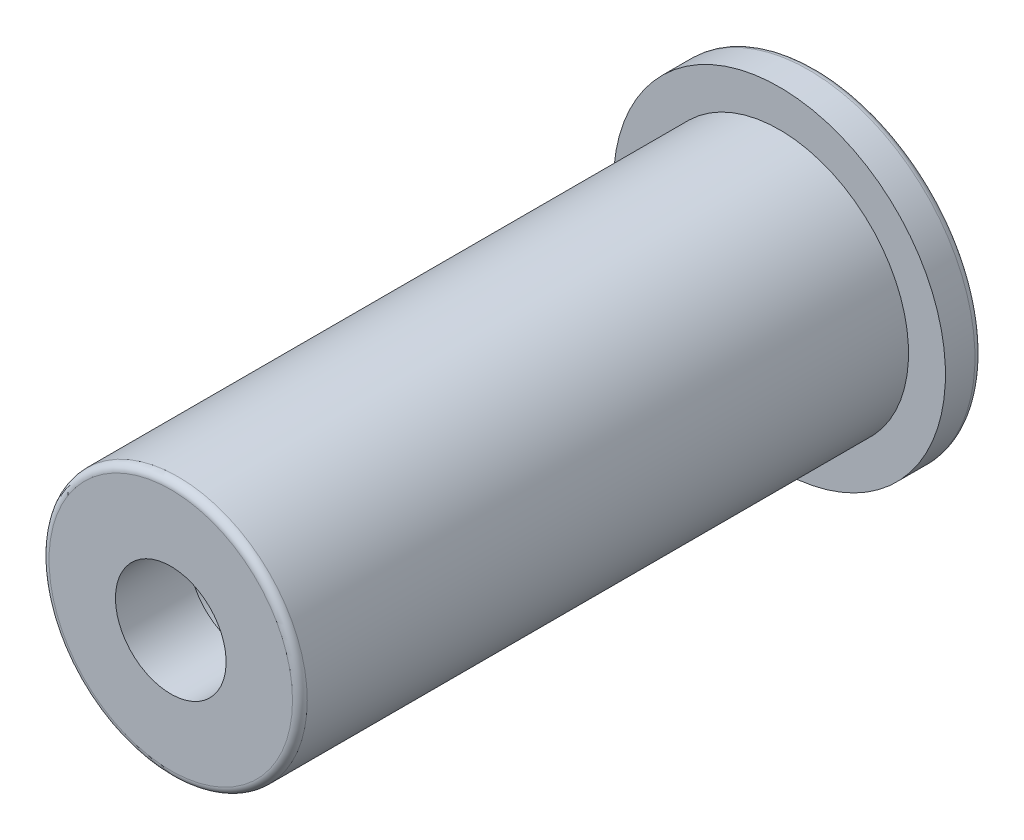
SolidWorks part; units mm, degrees
ref_plane "Спереди" through (0, 0, 0) normal (0, 0, 1) x (1, 0, 0)
ref_plane "Сверху" through (0, 0, 0) normal (0, 1, 0) x (1, 0, 0)
ref_plane "Справа" through (0, 0, 0) normal (1, 0, 0) x (0, 0, -1)
sketch "Эскиз1" plane through (0, 0, 0) normal (1, 0, 0) x (0, 0, -1)
  line L0 (-2, 7) -> (-2, 9)
  line L1 (-2, 9) -> (0, 9)
  line L2 (0, 9) -> (0, 4.5)
  line L3 (0, 4.5) -> (-31, 4.5)
  line L4 (-31, 4.5) -> (-31, 3)
  line L5 (-31, 3) -> (-35, 3)
  line L6 (-35, 3) -> (-35, 7)
  line L7 (-35, 7) -> (-2, 7)
  dimension "D1" = 4.5
  dimension "D2" = 7
  dimension "D3" = 2
  dimension "D4" = 9
  dimension "D5" = 3
  dimension "D6" = 4
  dimension "D7" = 33
ref_axis "Ось1" through (0, 0, -80.9) along (0, 0, 1)
revolve "Повернуть1" add sketch "Эскиз1" angle 360 about axis through (0, 0, -80.9) along (0, 0, 1)
fillet "Скругление1" radius 0.4 2 edges at (-7, 0, 35) (-9, 0, 0)
